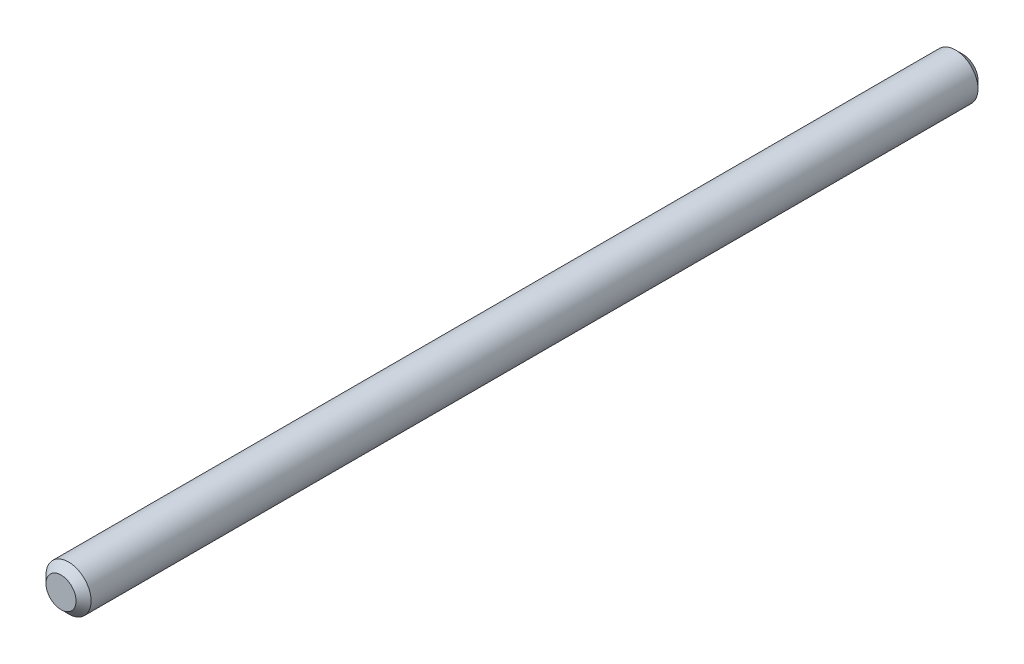
SolidWorks part; units mm, degrees
ref_plane "Face" through (0, 0, 0) normal (0, 0, 1) x (1, 0, 0)
ref_plane "Dessus" through (0, 0, 0) normal (0, 1, 0) x (1, 0, 0)
ref_plane "Droite" through (0, 0, 0) normal (1, 0, 0) x (0, 0, -1)
sketch "Esquisse1" plane through (0, 0, 0) normal (0, 0, 1) x (1, 0, 0)
  circle A0 centre (0, 0) radius 1.5
extrude "Base-Extrusion" add sketch "Esquisse1" along normal blind 60
chamfer "Chanfrein1" distance 0.5 angle 45 2 edges at (1.5, 0, 0) (1.5, 0, 60)
